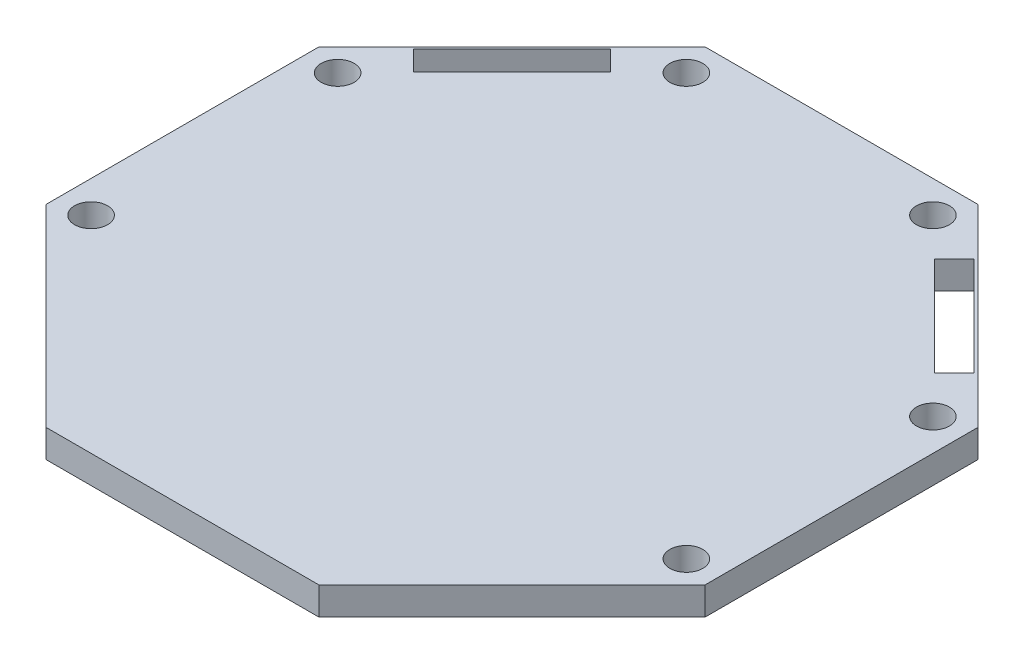
SolidWorks part; units mm, degrees
ref_plane "Front Plane" through (0, 0, 0) normal (0, 0, 1) x (1, 0, 0)
ref_plane "Top Plane" through (0, 0, 0) normal (0, 1, 0) x (1, 0, 0)
ref_plane "Right Plane" through (0, 0, 0) normal (1, 0, 0) x (0, 0, -1)
sketch "Sketch1" plane through (0, 0, 0) normal (0, 1, 0) x (1, 0, 0)
  line L0 (4.4681, 46.4957) -> (6.2641, 44.6996)
  line L1 (59.944, 42.3868) -> (42.3868, 59.944)
  line L2 (42.3868, 59.944) -> (17.5572, 59.944)
  line L3 (17.5572, 59.944) -> (0, 42.3868)
  line L4 (0, 42.3868) -> (0, 17.5572)
  line L5 (0, 17.5572) -> (17.5572, 0)
  line L6 (17.5572, 0) -> (42.3868, 0)
  line L7 (42.3868, 0) -> (59.944, 17.5572)
  line L8 (59.944, 17.5572) -> (59.944, 42.3868)
  line L9 (4.4681, 46.4957) -> (13.4483, 55.4759)
  line L10 (6.2641, 44.6996) -> (15.2444, 53.6799)
  line L11 (13.4483, 55.4759) -> (15.2444, 53.6799)
  line L12 (8.7786, 51.1654) -> (10.7543, 49.1897)
  line L13 (29.972, 59.944) -> (29.972, 0) construction
  line L14 (53.6799, 44.6996) -> (44.6996, 53.6799)
  line L15 (46.4957, 55.4759) -> (44.6996, 53.6799)
  line L16 (55.4759, 46.4957) -> (46.4957, 55.4759)
  line L17 (55.4759, 46.4957) -> (53.6799, 44.6996)
  circle A0 centre (29.972, 29.972) radius 29.972 construction
  point P15 (14.3464, 54.5779)
  point P24 (45.5976, 54.5779)
  dimension "D1" = 17.5572
  dimension "D2" = 12.7
  dimension "D3" = 42.3868
  dimension "D4" = 360
  dimension "D5" = 2.54
  dimension "D6" = 1.524
  dimension "D7" = 90
  dimension "D8" = 54.5779
  dimension "D9" = 14.3464
  dimension "D10" = 45.5976
extrude "Boss-Extrude1" add sketch "Sketch1" along normal blind 2.54
hole_wizard "Ø3.0mm Dowel Hole1" positions "Sketch2" profile "Sketch3" hole size "Ø3.0" standard "ANSI Metric"
sketch "Sketch2" plane through (0, 2.54, 0) normal (0, 1, 0) x (1, 0, 0)
  line L0 (0, 42.3868) -> (0, 17.5572) construction
  line L1 (0, 17.5572) -> (17.5572, 0) construction
  line L2 (17.5572, 59.944) -> (0, 42.3868) construction
  line L3 (42.3868, 59.944) -> (17.5572, 59.944) construction
  line L4 (59.944, 42.3868) -> (42.3868, 59.944) construction
  line L5 (59.944, 17.5572) -> (59.944, 42.3868) construction
  line L6 (42.3868, 0) -> (59.944, 17.5572) construction
  point P0 (2.9, 18.7584)
  point P7 (57.044, 18.7584)
  point P9 (2.9, 41.1856)
  point P11 (57.044, 41.1856)
  point P13 (18.7584, 57.044)
  point P15 (41.1856, 57.044)
  dimension "D1" = 2.9
  dimension "D2" = 2.9
  dimension "D3" = 2.9
  dimension "D4" = 2.9
  dimension "D5" = 2.9
  dimension "D6" = 2.9
  dimension "D7" = 2.9
  dimension "D8" = 2.9
  dimension "D9" = 2.9
  dimension "D10" = 2.9
  dimension "D11" = 2.9
  dimension "D12" = 2.9
sketch "Sketch3" plane through (2.9, 2.54, -18.7584) normal (1, 0, 0) x (0, 0, 1)
  line L0 (0, 0) -> (0, 8.9013)
  line L1 (0, 8.9013) -> (1.5, 8)
  line L2 (1.5, 8) -> (1.5, 0)
  line L5 (1.5, 0) -> (0, 0)
  line L10 (0, 8.9013) -> (-1.5, 8) construction
  line L11 (0, -6.35) -> (0, 107.95) construction
  dimension "Hole Dia." = 3
  dimension "Hole Depth" = 8
  dimension "Drill Angle" = 118
